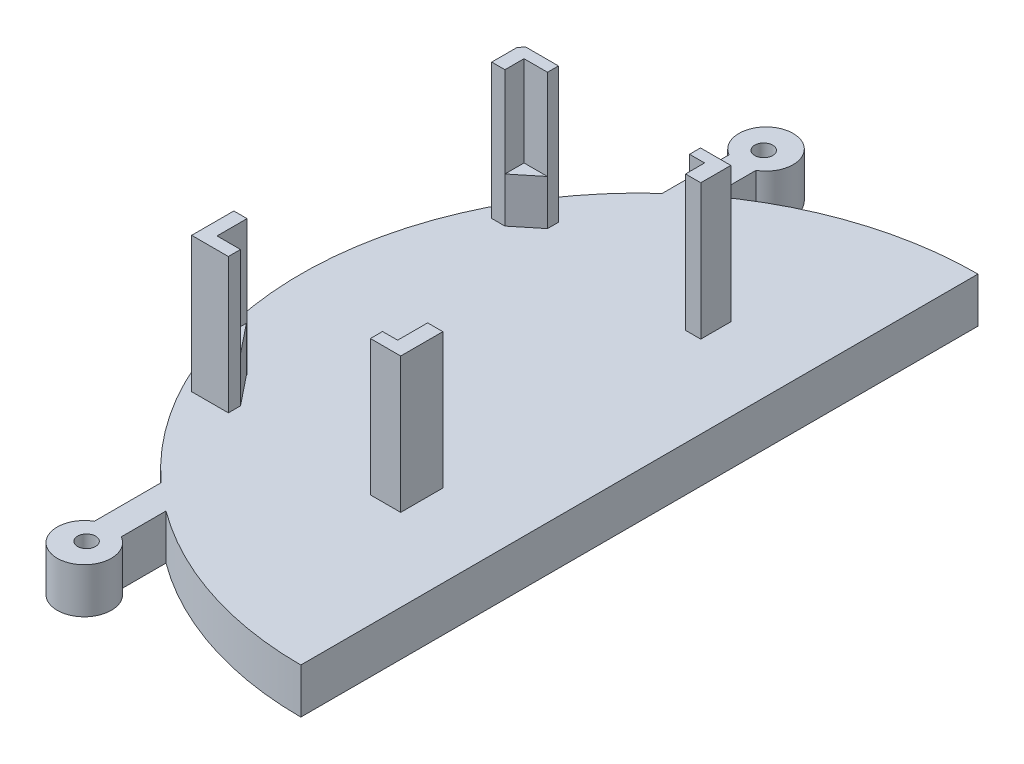
SolidWorks part; units mm, degrees
ref_plane "Ebene vorne" through (0, 0, 0) normal (0, 0, 1) x (1, 0, 0)
ref_plane "Ebene oben" through (0, 0, 0) normal (0, 1, 0) x (1, 0, 0)
ref_plane "Ebene rechts" through (0, 0, 0) normal (1, 0, 0) x (0, 0, -1)
sketch "Skizze1" plane through (0, 0, 0) normal (0, 1, 0) x (1, 0, 0)
  line L0 (0, 0) -> (0, -75)
  line L1 (0, -37.5) -> (-48.465, -37.5) construction
  arc A1 (0, -75) -> (0, 0) centre (0, -37.5) cw
  dimension "D1" = 75
extrude "Aufsatz-Linear austragen1" add sketch "Skizze1" along normal blind 5
sketch "Skizze4" plane through (0, 5, 0) normal (0, 1, 0) x (1, 0, 0)
  line L0 (-22.2381, -7.3053) -> (-22.2381, 0.2519)
  line L1 (-25.2207, 0.2519) -> (-22.2381, 0.2519)
  line L2 (-25.2207, 0.2519) -> (-25.2207, -9.7481)
  line L3 (-25.2207, -9.7481) -> (-22.2381, -9.7481)
  line L4 (-22.2381, -9.7481) -> (-22.2381, -7.3053)
  line L5 (-22.2381, -67.6947) -> (-22.2381, -75.2519)
  line L6 (-22.2381, -75.2519) -> (-25.2207, -75.2519)
  line L7 (-25.2207, -75.2519) -> (-25.2207, -65.2519)
  line L8 (-25.2207, -65.2519) -> (-22.2381, -65.2519)
  line L9 (-22.2381, -65.2519) -> (-22.2381, -67.6947)
  line L10 (0, -75) -> (0, 0) construction
  arc A0 (0, 0) -> (0, -75) centre (0, -37.5) ccw construction
  dimension "D1" = 22.2381
extrude "Aufsatz-Linear austragen2" add sketch "Skizze4" against normal blind 5
sketch "Skizze5" plane through (0, 5, 0) normal (0, 1, 0) x (1, 0, 0)
  line L0 (-22.2381, 0.2519) -> (-25.2207, 0.2519) construction
  line L1 (-25.2207, -75.2519) -> (-22.2381, -75.2519) construction
  circle A0 centre (-23.7294, 0.2519) radius 3
  circle A1 centre (-23.7294, -75.2519) radius 3
extrude "Aufsatz-Linear austragen3" add sketch "Skizze5" against normal blind 5
sketch "Skizze6" plane through (0, 5, 0) normal (0, 1, 0) x (1, 0, 0)
  circle A0 centre (-23.7294, 0) radius 1
  circle A1 centre (-23.7294, -75) radius 1
extrude "Schnitt-Linear austragen3" cut sketch "Skizze6" against normal blind 5
sketch "Skizze7" plane through (0, 5, 0) normal (0, 1, 0) x (1, 0, 0)
  line L12 (-32.2587, -18.8309) -> (-32.2587, -54.8309)
  line L13 (-32.2587, -54.8309) -> (-9.107, -54.8309)
  line L14 (-9.107, -54.8309) -> (-9.107, -18.2696)
  line L15 (-9.107, -18.2696) -> (-31.8447, -18.2696)
  line L16 (-31.8447, -18.2696) -> (-32.2587, -18.8309)
extrude "Aufsatz-Linear austragen4" add sketch "Skizze7" along normal blind 15
sketch "Skizze8" plane through (0, 20, 0) normal (0, 1, 0) x (1, 0, 0)
  line L0 (-30.7938, -19.4852) -> (-10.7938, -19.4852)
  line L1 (-30.7938, -19.4852) -> (-30.7938, -53.4852)
  line L2 (-30.7938, -53.4852) -> (-10.7938, -53.4852)
  line L3 (-10.7938, -19.4852) -> (-10.7938, -53.4852)
extrude "Schnitt-Linear austragen4" cut sketch "Skizze8" against normal blind 15
sketch "Skizze9" plane through (0, 20, 0) normal (0, 1, 0) x (1, 0, 0)
  line L0 (-28.1946, -53.4852) -> (-28.1946, -54.8309)
  line L1 (-30.7938, -53.4852) -> (-10.7938, -53.4852) construction
  line L2 (-32.2587, -54.8309) -> (-9.107, -54.8309) construction
  line L3 (-28.1946, -54.8309) -> (-12.4627, -54.8309)
  line L4 (-12.4627, -54.8309) -> (-12.4627, -53.4852)
  line L5 (-12.4627, -53.4852) -> (-28.1946, -53.4852)
  line L6 (-30.7938, -50.1608) -> (-30.7938, -21.5987)
  line L7 (-30.7938, -19.4852) -> (-30.7938, -53.4852) construction
  line L8 (-30.7938, -21.5987) -> (-32.2587, -21.5987)
  line L9 (-32.2587, -18.8309) -> (-32.2587, -54.8309) construction
  line L10 (-32.2587, -21.5987) -> (-32.2587, -50.1608)
  line L11 (-32.2587, -50.1608) -> (-30.7938, -50.1608)
  line L12 (-12.4627, -19.4852) -> (-28.1946, -19.4852)
  line L13 (-10.7938, -19.4852) -> (-30.7938, -19.4852) construction
  line L14 (-28.1946, -19.4852) -> (-28.1946, -18.2696)
  line L15 (-9.107, -18.2696) -> (-31.8447, -18.2696) construction
  line L16 (-28.1946, -18.2696) -> (-12.4627, -18.2696)
  line L17 (-12.4627, -18.2696) -> (-12.4627, -19.4852)
  line L18 (-10.7938, -21.5987) -> (-9.107, -21.5987)
  line L19 (-10.7938, -53.4852) -> (-10.7938, -19.4852) construction
  line L20 (-9.107, -54.8309) -> (-9.107, -18.2696) construction
  line L21 (-9.107, -21.5987) -> (-9.107, -50.1608)
  line L22 (-9.107, -50.1608) -> (-10.7938, -50.1608)
  line L23 (-10.7938, -50.1608) -> (-10.7938, -21.5987)
extrude "Schnitt-Linear austragen5" cut sketch "Skizze9" against normal blind 15
sketch "Skizze10" plane through (0, 5, 0) normal (0, 1, 0) x (1, 0, 0)
  line L0 (-28.1946, -53.4852) -> (-30.7938, -50.2348)
  line L1 (-30.7938, -50.1608) -> (-30.7938, -53.4852) construction
  line L2 (-30.7938, -50.2348) -> (-30.7938, -53.4852)
  line L3 (-30.7938, -53.4852) -> (-28.1946, -53.4852)
  line L4 (-30.7938, -21.5987) -> (-30.7938, -19.4852)
  line L5 (-30.7938, -19.4852) -> (-30.7938, -21.5987) construction
  line L6 (-30.7938, -19.4852) -> (-28.1946, -19.4852)
  line L7 (-28.1946, -19.4852) -> (-30.7938, -21.5987)
  line L8 (-12.4627, -19.4852) -> (-10.7938, -19.4852)
  line L9 (-10.7938, -19.4852) -> (-12.4627, -19.4852) construction
  line L10 (-10.7938, -19.4852) -> (-10.7938, -21.5987)
  line L11 (-10.7938, -21.5987) -> (-12.4627, -19.4852)
  line L12 (-12.4627, -53.4852) -> (-10.7938, -53.4852)
  line L13 (-12.4627, -53.4852) -> (-10.7938, -53.4852) construction
  line L14 (-10.7938, -53.4852) -> (-10.7938, -50.2348)
  line L15 (-10.7938, -53.4852) -> (-10.7938, -50.1608) construction
  line L16 (-10.7938, -50.2348) -> (-12.4627, -53.4852)
extrude "Aufsatz-Linear austragen5" add sketch "Skizze10" along normal blind 5
